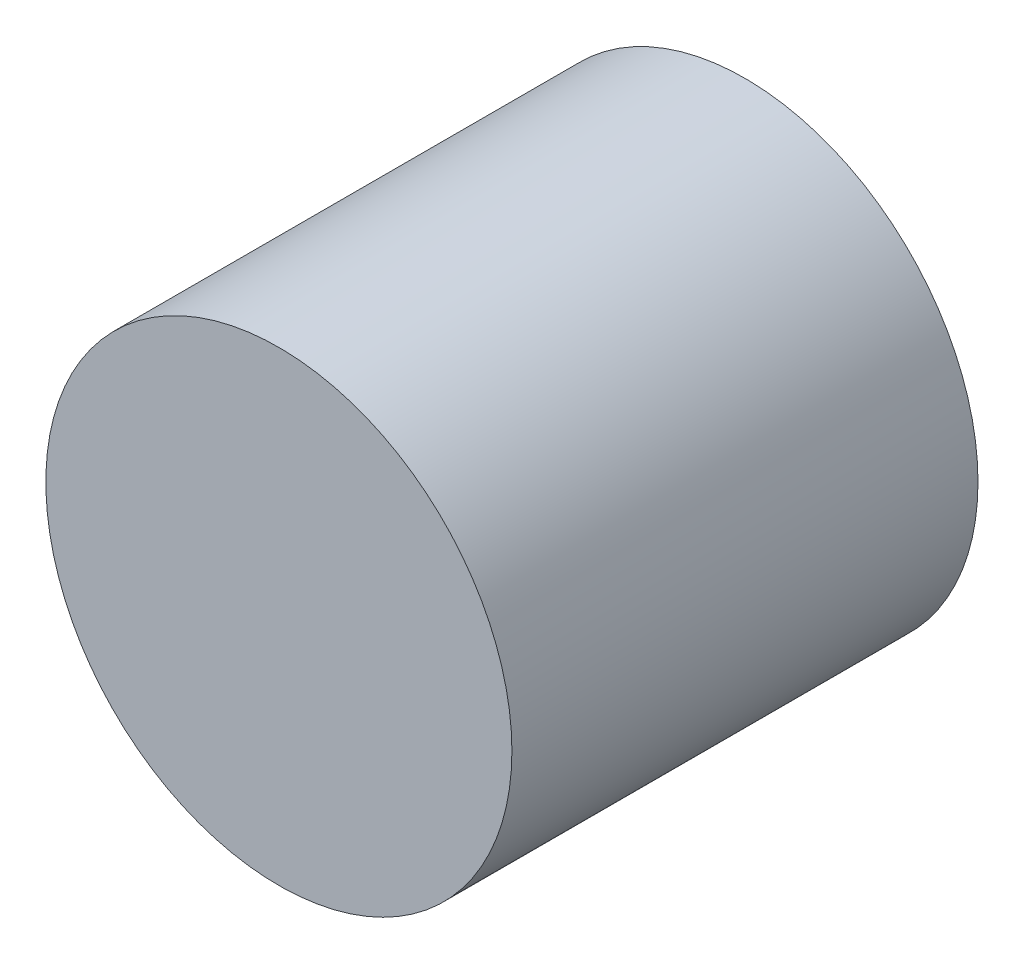
SolidWorks part; units mm, degrees
ref_plane "Front Plane" through (0, 0, 0) normal (0, 0, 1) x (1, 0, 0)
ref_plane "Top Plane" through (0, 0, 0) normal (0, 1, 0) x (1, 0, 0)
ref_plane "Right Plane" through (0, 0, 0) normal (1, 0, 0) x (0, 0, -1)
sketch "Sketch1" plane through (0, 0, 0) normal (0, 0, 1) x (1, 0, 0)
  circle A0 centre (-25.5387, 9.4174) radius 25.4
  dimension "D1" = 50.8
extrude "Boss-Extrude1" add sketch "Sketch1" along normal blind 50.8
